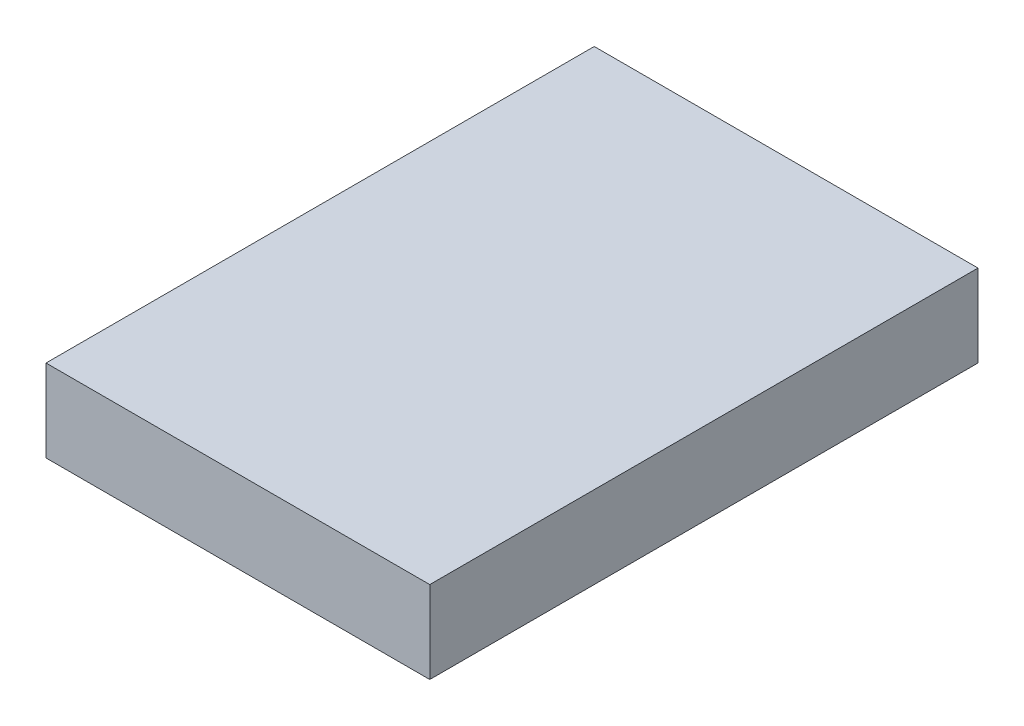
SolidWorks part; units mm, degrees
ref_plane "Front Plane" through (0, 0, 0) normal (0, 0, 1) x (1, 0, 0)
ref_plane "Top Plane" through (0, 0, 0) normal (0, 1, 0) x (1, 0, 0)
ref_plane "Right Plane" through (0, 0, 0) normal (1, 0, 0) x (0, 0, -1)
sketch "Sketch2" plane through (0, 0, 0) normal (0, 1, 0) x (1, 0, 0)
  line L1 (-35, -50) -> (35, -50)
  line L2 (-35, -50) -> (-35, 50)
  line L3 (-35, 50) -> (35, 50)
  line L4 (35, -50) -> (35, 50)
  line L5 (-35, -50) -> (35, 50) construction
  line L6 (-35, 50) -> (35, -50) construction
  point P0 (0, 0)
  dimension "D1" = 100
  dimension "D2" = 70
extrude "Boss-Extrude1" add sketch "Sketch2" along normal blind 15
